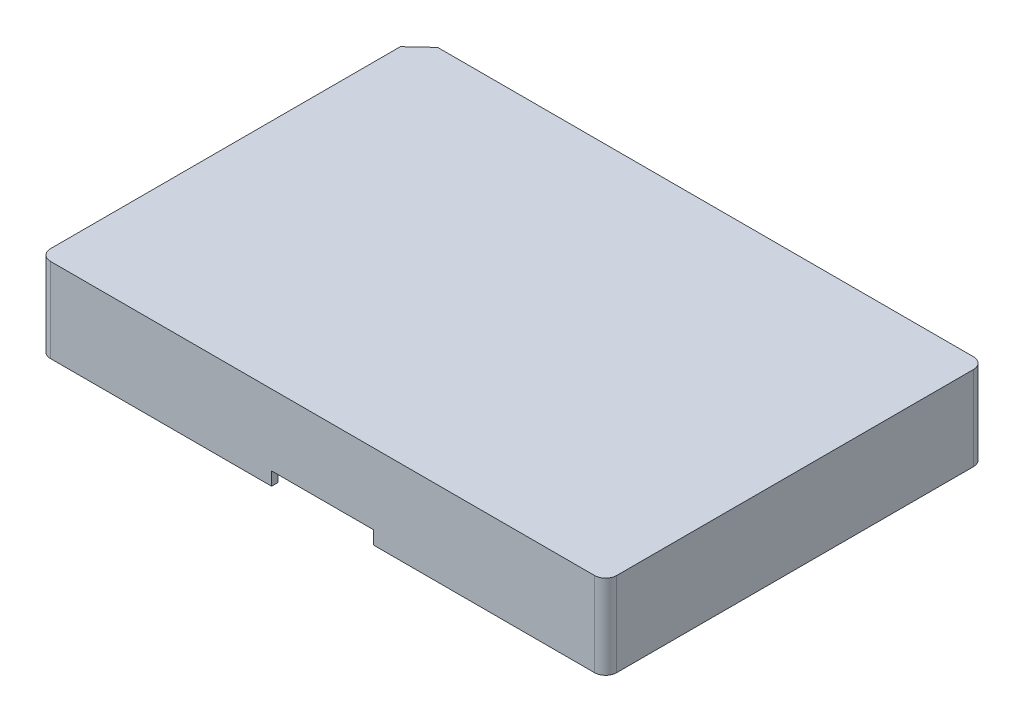
SolidWorks part; units mm, degrees
ref_plane "Front Plane" through (0, 0, 0) normal (0, 0, 1) x (1, 0, 0)
ref_plane "Top Plane" through (0, 0, 0) normal (0, 1, 0) x (1, 0, 0)
ref_plane "Right Plane" through (0, 0, 0) normal (1, 0, 0) x (0, 0, -1)
sketch "Sketch3" plane through (0, 0, 0) normal (0, 1, 0) x (1, 0, 0)
  line L0 (-58.2884, -117.2853) -> (67.4616, -117.2853)
  line L5 (67.4616, -117.2853) -> (67.4616, -33.7853)
  line L6 (67.4616, -33.7853) -> (-54.5384, -33.7853)
  line L7 (-54.5384, -33.7853) -> (-58.2884, -37.2853)
  line L8 (-58.2884, -37.2853) -> (-58.2884, -117.2853)
  line L9 (68.4616, -32.7853) -> (-54.9325, -32.7853)
  line L10 (-54.9325, -32.7853) -> (-59.2884, -36.8508)
  line L11 (-59.2884, -36.8508) -> (-59.2884, -118.2853)
  line L12 (-59.2884, -118.2853) -> (68.4616, -118.2853)
  line L13 (68.4616, -118.2853) -> (68.4616, -32.7853)
  dimension "D1" = 83.5
  dimension "D2" = 122
  dimension "D3" = 1
  dimension "D4" = 125.75
  dimension "D5" = 80
extrude "Boss-Extrude1" add sketch "Sketch3" along normal blind 19 contours L11 L12 L13 L9 L10
sketch "Sketch4" plane through (0, 0, 0) normal (0, 0, 1) x (1, 0, 0)
  line L1 (-6.9134, 3) -> (16.0866, 3)
  line L2 (-6.9134, 3) -> (-6.9134, 0)
  line L3 (-6.9134, 0) -> (16.0866, 0)
  line L4 (16.0866, 3) -> (16.0866, 0)
  line L7 (-59.2884, 0) -> (68.4616, 0) construction
  point P4 (4.5866, 0)
  point P7 (4.5866, 0)
  dimension "D1" = 23
  dimension "D2" = 3
fillet "Fillet1" radius 2.5 3 edges at (-59.2884, 9.5, 118.2853) (68.4616, 9.5, 32.7853) (68.4616, 9.5, 118.2853)
shell "Shell1" thickness 1.5
extrude "Cut-Extrude1" cut sketch "Sketch4" against normal through all both and the other way through all contours L3 L4 L1 L2
